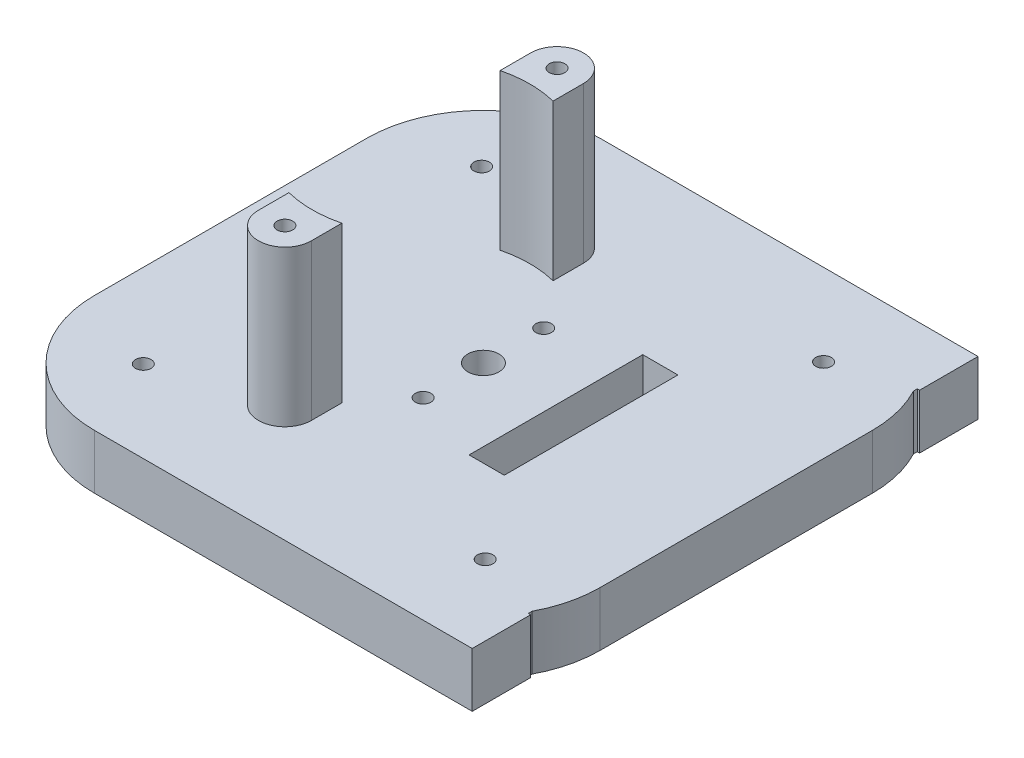
SolidWorks part; units mm, degrees
ref_plane "Front Plane" through (0, 0, 0) normal (0, 0, 1) x (1, 0, 0)
ref_plane "Top Plane" through (0, 0, 0) normal (0, 1, 0) x (1, 0, 0)
ref_plane "Right Plane" through (0, 0, 0) normal (1, 0, 0) x (0, 0, -1)
sketch "Sketch1" plane through (0, 0, 0) normal (0, 1, 0) x (1, 0, 0)
  line L20 (41.9014, -22.1907) -> (41.9014, 12.8093)
  line L21 (40.1679, -29.6907) -> (40.1679, -29.1907)
  line L22 (40.1679, 19.8093) -> (40.1679, 20.3093)
  line L23 (40.1679, 20.3093) -> (40.4638, 20.3093)
  line L24 (40.4638, 20.3093) -> (40.4638, 27.8093)
  line L25 (40.4638, 27.8093) -> (-8.0986, 27.8093)
  line L26 (-23.0986, 12.8093) -> (-23.0986, -22.1907)
  line L27 (-8.0986, -37.1907) -> (40.4638, -37.1907)
  line L28 (40.4638, -37.1907) -> (40.4638, -29.6907)
  line L29 (40.4638, -29.6907) -> (40.1679, -29.6907)
  arc A22 (40.4638, -28.5987) -> (41.9014, -22.1907) centre (26.9014, -22.1907) ccw
  arc A23 (41.9014, 12.8093) -> (40.4638, 19.2172) centre (26.9014, 12.8093) ccw
  arc A24 (40.1679, -29.1907) -> (40.4638, -28.5987) centre (26.9014, -22.1907) ccw
  arc A25 (40.4638, 19.2172) -> (40.1679, 19.8093) centre (26.9014, 12.8093) ccw
  arc A26 (-8.0986, 27.8093) -> (-23.0986, 12.8093) centre (-8.0986, 12.8093) ccw
  arc A27 (-23.0986, -22.1907) -> (-8.0986, -37.1907) centre (-8.0986, -22.1907) ccw
  circle A28 centre (31.3701, -26.4334) radius 1
  circle A29 centre (-12.3412, -26.6595) radius 1
  circle A30 centre (-12.5673, 17.0519) radius 1
  circle A31 centre (31.144, 17.278) radius 1
  circle A32 centre (9.4014, -4.6907) radius 25.5
  circle A33 centre (9.4014, -4.6907) radius 2
  dimension "D1" = 48.5624
extrude "Boss-Extrude4" add sketch "Sketch1" along normal blind 7 contours A32 A33 | L26 A27 L27 L28 L29 L21 A24 A22 L20 A23 A25 L22 L23 L24 L25 A26 A32 A31 A30 A29 A28
sketch "Sketch3" plane through (0, 7, 0) normal (0, 1, 0) x (1, 0, 0)
  line L6 (40.2211, 19.7105) -> (40.2234, 20.2105)
  line L14 (-2.0466, -18.2344) -> (-2.0466, -22.1535)
  line L15 (4.7534, -22.1535) -> (4.7534, -18.2344)
  line L16 (4.7327, 8.9274) -> (4.7327, 12.8465)
  line L17 (-2.0673, 12.8465) -> (-2.0673, 8.9274)
  arc A23 (39.9973, -29.289) -> (40.2959, -28.6983) centre (26.7629, -22.2285) ccw
  arc A24 (40.5143, 19.1171) -> (40.2211, 19.7105) centre (26.9228, 12.7711) ccw
  arc A27 (-0.3966, -22.1545) -> (3.1034, -22.1525) centre (1.3534, -22.1535) ccw
  arc A28 (3.1034, -22.1525) -> (-0.3966, -22.1545) centre (1.3534, -22.1535) ccw
  arc A29 (-0.4173, 12.8455) -> (3.0827, 12.8475) centre (1.3327, 12.8465) ccw
  arc A30 (3.0827, 12.8475) -> (-0.4173, 12.8455) centre (1.3327, 12.8465) ccw
  arc A31 (-2.0466, -18.2344) -> (4.7534, -18.2344) centre (1.3534, -4.6535) ccw
  arc A32 (-2.0466, -22.1535) -> (4.7534, -22.1535) centre (1.3534, -22.1535) ccw
  arc A33 (-0.3966, -22.1535) -> (3.1034, -22.1535) centre (1.3534, -22.1535) ccw
  arc A34 (3.1034, -22.1535) -> (-0.3966, -22.1535) centre (1.3534, -22.1535) ccw
  arc A35 (4.7327, 8.9274) -> (-2.0673, 8.9274) centre (1.3327, -4.6535) ccw
  arc A36 (4.7327, 12.8465) -> (-2.0673, 12.8465) centre (1.3327, 12.8465) ccw
  arc A37 (3.0827, 12.8465) -> (-0.4173, 12.8465) centre (1.3327, 12.8465) ccw
  arc A38 (-0.4173, 12.8465) -> (3.0827, 12.8465) centre (1.3327, 12.8465) ccw
  circle A39 centre (1.3327, 12.8465) radius 1
  circle A40 centre (1.3534, -22.1535) radius 1
  dimension "D1" = 2
extrude "Boss-Extrude6" add sketch "Sketch3" along normal blind 20 contours L16 A36 L17 A35 A30 A29 | A29 A30 A39 | L14 A32 L15 A31 A28 A27 | A27 A28 A40
sketch "Sketch4" plane through (0, 0, 0) normal (0, -1, 0) x (1, 0, 0)
  line L1 (22.2414, -5.4693) -> (19.7198, -5.4693)
  line L2 (22.2414, 14.8507) -> (19.7198, 14.8507)
  line L3 (19.7198, -5.4693) -> (19.7198, 14.8507)
  line L4 (9.4014, -3.0593) -> (9.4014, 12.4407) construction
  line L5 (23.2414, -6.4693) -> (23.2414, 15.8507)
  line L6 (23.2414, 15.8507) -> (18.7198, 15.8507)
  line L7 (18.7198, -6.4693) -> (18.7198, 15.8507)
  line L8 (23.2414, -6.4693) -> (18.7198, -6.4693)
  line L9 (22.2414, -5.4693) -> (22.2414, 14.8507) construction
  circle A0 centre (9.4014, -3.0593) radius 1
  circle A1 centre (9.4014, 12.4407) radius 1
  circle A2 centre (9.4014, 4.6907) radius 2 construction
  circle A3 centre (9.4014, 4.6907) radius 2
  dimension "D1" = 2
  dimension "D2" = 2
  dimension "D3" = 1
extrude "Cut-Extrude2" cut sketch "Sketch4" against normal blind 10
